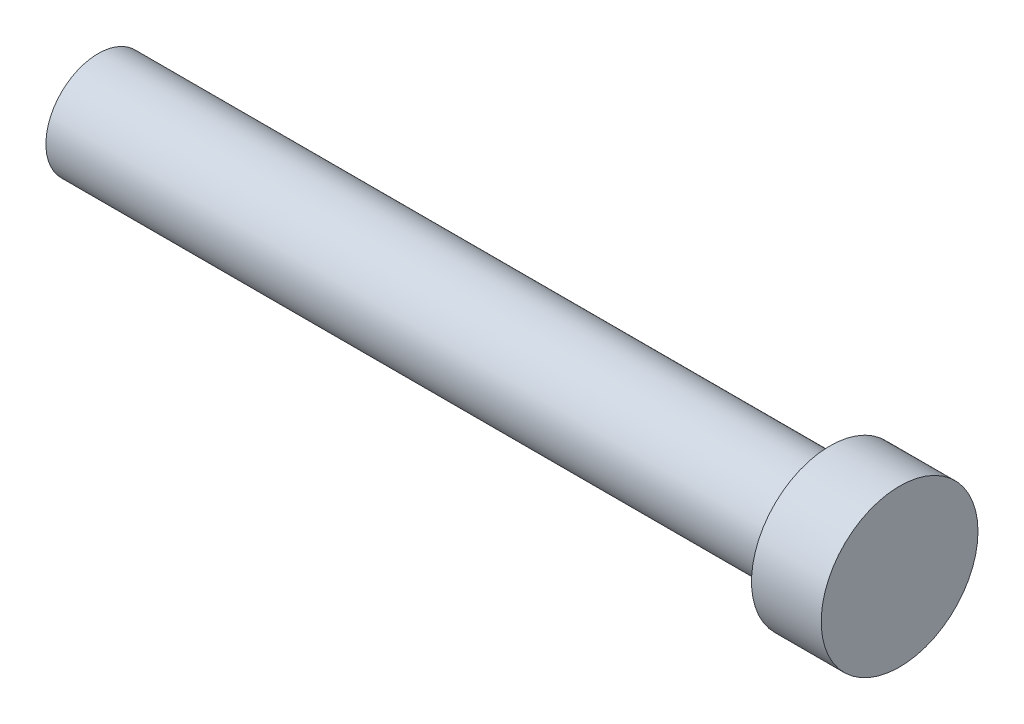
SolidWorks part; units mm, degrees
ref_plane "Front Plane" through (0, 0, 0) normal (0, 0, 1) x (1, 0, 0)
ref_plane "Top Plane" through (0, 0, 0) normal (0, 1, 0) x (1, 0, 0)
ref_plane "Right Plane" through (0, 0, 0) normal (1, 0, 0) x (0, 0, -1)
sketch "Sketch2" plane through (0, 0, 0) normal (1, 0, 0) x (0, 0, -1)
  circle A0 centre (0, 0) radius 15
  dimension "D1" = 30
extrude "Boss-Extrude1" add sketch "Sketch2" along normal blind 210
sketch "Sketch3" plane through (210, 0, 0) normal (1, 0, 0) x (0, 0, -1)
  circle A0 centre (0, 0) radius 22.5
  dimension "D1" = 45
extrude "Boss-Extrude2" add sketch "Sketch3" along normal blind 20
